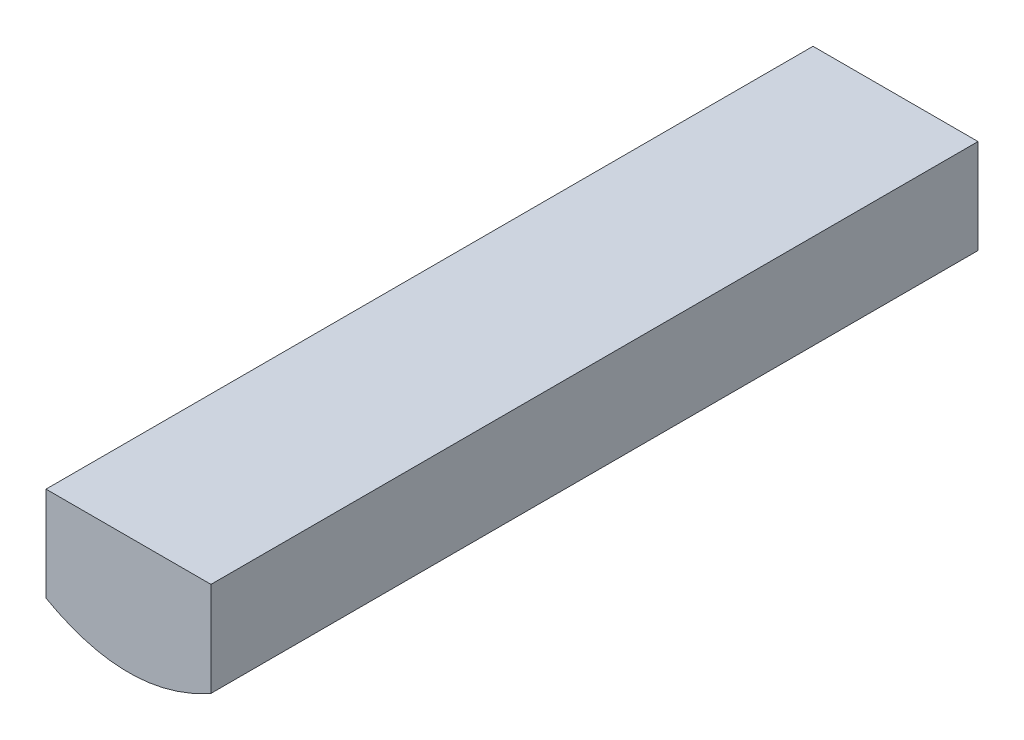
SolidWorks part; units mm, degrees
ref_plane "Front Plane" through (0, 0, 0) normal (0, 0, 1) x (1, 0, 0)
ref_plane "Top Plane" through (0, 0, 0) normal (0, 1, 0) x (1, 0, 0)
ref_plane "Right Plane" through (0, 0, 0) normal (1, 0, 0) x (0, 0, -1)
sketch "Sketch2" plane through (0, 0, 0) normal (0, 0, 1) x (1, 0, 0)
  line L0 (-127, 127) -> (127, 127)
  spline S0 degree 2 poles (-143.0272, 161.0769) (0, -161.0769) (143.0272, 161.0769) knots 0 0 0 1 1 1 construction
  spline S1 degree 2 poles (-127, 127) (0, -127) (127, 127) knots 0.056028 0.056028 0.056028 0.943972 0.943972 0.943972
extrude "Boss-Extrude2" add sketch "Sketch2" along normal blind 331.382
sketch "Sketch5" plane through (0, 0, 331.382) normal (0, 0, 1) x (1, 0, 0)
  line L0 (0, 0) -> (0, 10) construction
  line L1 (-130, 130) -> (130, 130)
  line L2 (-130, 130) -> (-130, 10)
  line L3 (-130, 10) -> (130, 10)
  line L4 (130, 130) -> (130, 10)
  dimension "D1" = 10
  dimension "D2" = 260
  dimension "D3" = 120
extrude "Cut-Extrude4" cut sketch "Sketch5" against normal through all
sketch "Sketch6" plane through (0, 0, 331.382) normal (0, 0, 1) x (1, 0, 0)
  line L1 (-35.6371, 10) -> (35.6371, 10)
  line L2 (-35.6371, 10) -> (-35.6371, 50.8)
  line L3 (-35.6371, 50.8) -> (35.6371, 50.8)
  line L4 (35.6371, 10) -> (35.6371, 50.8)
  dimension "D1" = 40.8
extrude "Boss-Extrude3" add sketch "Sketch6" against normal blind 331.382
